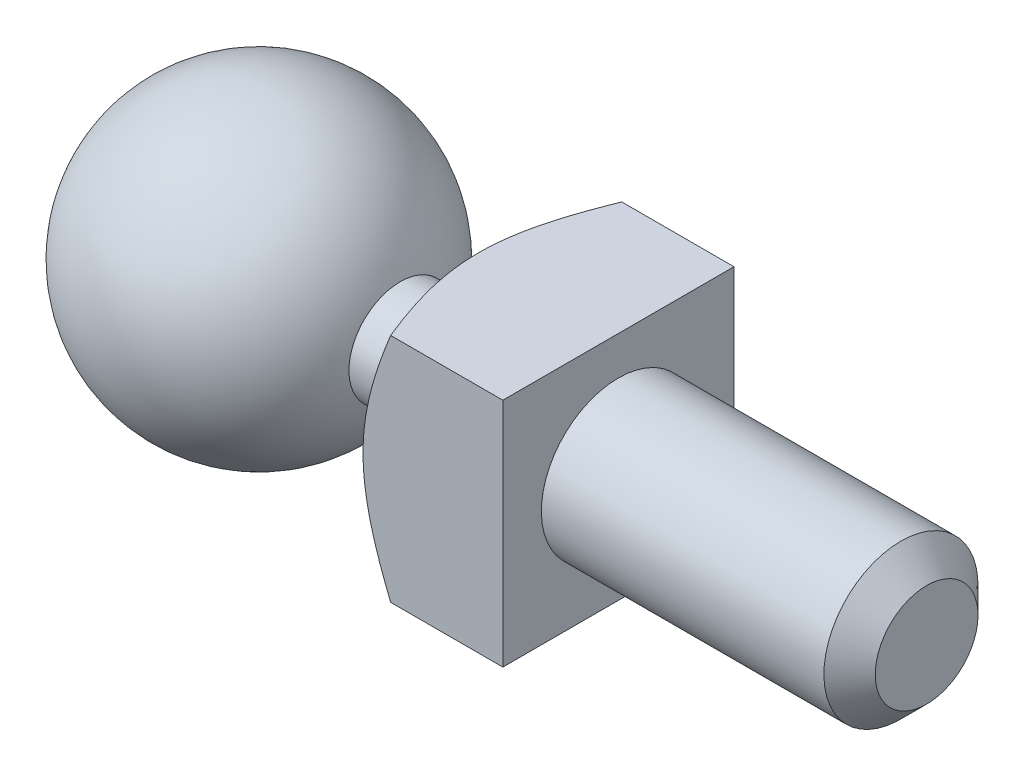
SolidWorks part; units mm, degrees
ref_plane "Plan de face" through (0, 0, 0) normal (0, 0, 1) x (1, 0, 0)
ref_plane "Plan de dessus" through (0, 0, 0) normal (0, 1, 0) x (1, 0, 0)
ref_plane "Plan de droite" through (0, 0, 0) normal (1, 0, 0) x (0, 0, -1)
sketch "Esquisse1" plane through (0, 0, 0) normal (0, 0, 1) x (1, 0, 0)
  line L0 (2.7541, 1) -> (3.5566, 1)
  line L1 (13, 0) -> (-2.93, 0)
  line L2 (5, 3.5) -> (3.5566, 1)
  line L4 (5, 3.5) -> (7, 3.5)
  line L5 (7, 3.5) -> (7, 1.5)
  line L6 (7, 1.5) -> (13, 1.5)
  line L7 (13, 1.5) -> (13, 0)
  line L8 (13, 0) -> (0, 0) construction
  line L9 (0, 0) -> (-2.93, 0) construction
  arc A0 (2.7541, 1) -> (-2.93, 0) centre (0, 0) ccw
  dimension "D6" = 2.93
  dimension "D1" = 1.5
  dimension "D2" = 6
  dimension "D3" = 2
  dimension "D4" = 5
  dimension "D5" = 1
  dimension "D7" = 3.5
  dimension "D8" = 60
revolve "Révolution1" add sketch "Esquisse1" angle 360 about L1
cosmetic thread "Représentation de filetage1" parameters "D2"=2.439
sketch "Esquisse2" plane through (7, 0, 0) normal (1, 0, 0) x (0, 0, -1)
  line L0 (0, 0) -> (3.5, 0) construction
  line L1 (-2.681, 2.25) -> (2.681, 2.25)
  line L2 (-2.681, 2.25) -> (-2.681, 3.5)
  line L3 (-2.681, 3.5) -> (2.681, 3.5)
  line L4 (2.681, 2.25) -> (2.681, 3.5)
  line L5 (2.681, -2.25) -> (2.681, -3.5)
  line L6 (-2.681, -3.5) -> (2.681, -3.5)
  line L7 (-2.681, -2.25) -> (-2.681, -3.5)
  line L8 (-2.681, -2.25) -> (2.681, -2.25)
  circle A0 centre (0, 0) radius 3.5 construction
  dimension "D1" = 2.25
extrude "Enlèv. mat.-Extru.1" cut sketch "Esquisse2" against normal blind 3 contours L3 L4 L1 L2
sketch "Esquisse4" plane through (7, 0, 0) normal (1, 0, 0) x (0, 0, -1)
  line L0 (0, 2.25) -> (0, -2.25) construction
  line L1 (-2.681, 2.25) -> (2.681, 2.25) construction
  line L2 (2.681, -2.25) -> (-2.681, -2.25) construction
  line L3 (3.5, 2.25) -> (3.5, -2.25)
  line L4 (-2.25, 2.25) -> (-3.5, 2.25)
  line L5 (-2.25, 2.25) -> (-2.25, -2.25)
  line L6 (-2.25, -2.25) -> (-3.5, -2.25)
  line L7 (-3.5, 2.25) -> (-3.5, -2.25)
  line L8 (2.25, -2.25) -> (3.5, -2.25)
  line L9 (2.25, 2.25) -> (2.25, -2.25)
  line L10 (2.25, 2.25) -> (3.5, 2.25)
  arc A0 (-2.681, 2.25) -> (-2.681, -2.25) centre (0, 0) ccw construction
  dimension "D1" = 2.25
extrude "Enlèv. mat.-Extru.2" cut sketch "Esquisse4" against normal blind 2.75
chamfer "Chanfrein1" distance 0.5 angle 45 1 edges at (13, 1.5, 0)
